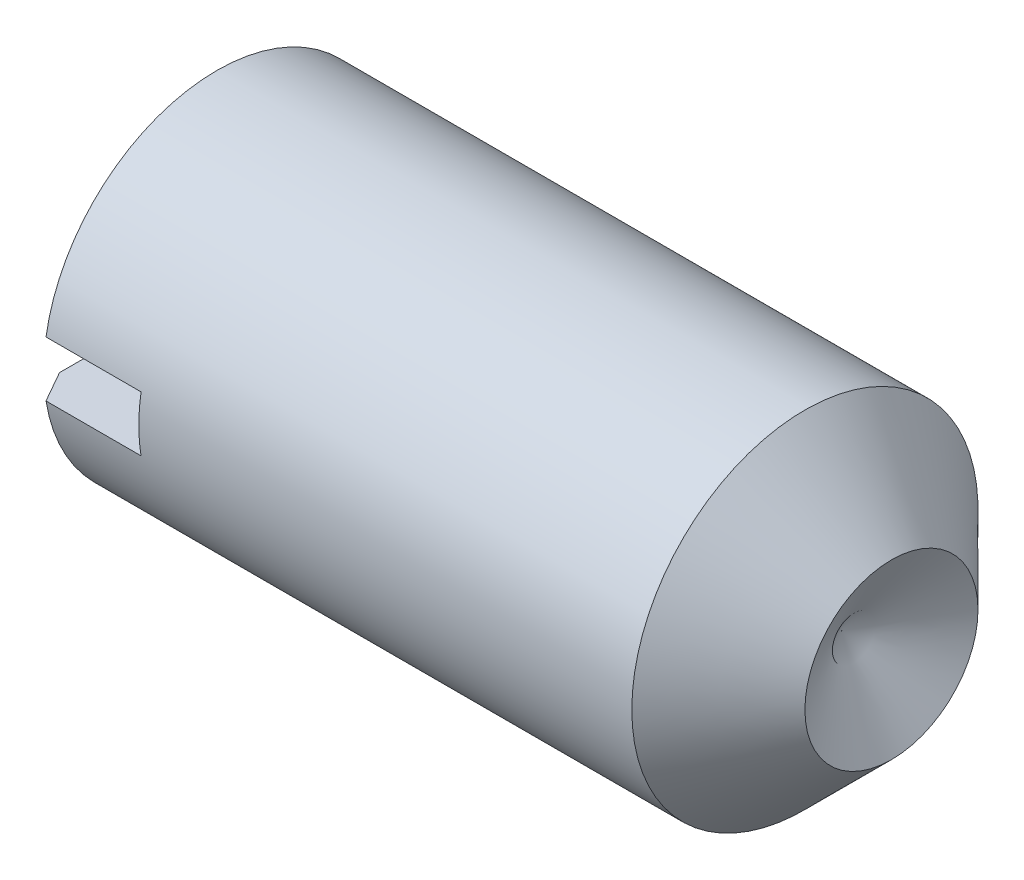
SolidWorks part; units mm, degrees
ref_plane "Plane1" through (0, 0, 0) normal (0, 0, 1) x (1, 0, 0)
ref_plane "Plane2" through (0, 0, 0) normal (0, 1, 0) x (1, 0, 0)
ref_plane "Plane3" through (0, 0, 0) normal (1, 0, 0) x (0, 0, -1)
sketch "BodySke" plane through (0, 0, 0) normal (0, 0, 1) x (1, 0, 0)
  line L0 (0.2569, -2.5) -> (47.1574, -2.5) construction
  line L1 (10, 1.25) -> (9.2783, 0)
  line L2 (0.2569, 2.5) -> (8.75, 2.5)
  line L3 (10, 1.25) -> (8.75, 2.5)
  line L4 (9.2783, 0) -> (0, 0)
  line L5 (-12.7, 0) -> (88.9, 0) construction
  line L6 (10, 1.25) -> (10, 19.05) construction
  line L7 (10, -1.25) -> (8.75, -2.5) construction
  line L8 (0.8, 12.7) -> (0.8, -3.175) construction
  line L9 (0, 0) -> (0, 2.055)
  line L10 (0, 2.055) -> (0.2569, 2.5)
  line L11 (0, -2.055) -> (0.2569, -2.5) construction
  line L12 (10, -1.25) -> (9.2783, 0) construction
  dimension "Length" = 10
  dimension "Diameter" = 5
  dimension "Drive_ch_ang" = 60
  dimension "Cup_ang" = 120
  dimension "Cup_dia" = 2.5
  dimension "Nose_ch_ang" = 45
  dimension "Advance" = 0.8
  dimension "Minor_dia" = 4.11
revolve "BaseBody" add sketch "BodySke"
cosmetic thread "ThreadCosmetic" [suppressed]
extrude "Slot" cut sketch "Sketch2" along normal blind 1.63
sketch "Sketch2" plane through (0, 0, 0) normal (1, 0, 0) x (0, 0, -1)
  line L1 (2.5, -0.4) -> (-2.5, -0.4)
  line L2 (2.5, -0.4) -> (2.5, 0.4)
  line L3 (2.5, 0.4) -> (-2.5, 0.4)
  line L4 (-2.5, -0.4) -> (-2.5, 0.4)
  dimension "D1" = 5
  dimension "D2" = 0.4
  dimension "Slot_width" = 0.8
  dimension "D3" = 2.5
sketch "ThdSchSke" plane through (0, 0, 0) normal (0, 0, 1) x (1, 0, 0)
  line L0 (0.2569, -2.055) -> (-0.0547, -2.5)
  line L1 (0.2569, -2.055) -> (0.5685, -2.5)
  line L2 (0.5685, -2.5) -> (0.5685, -3.125)
  line L3 (-3.175, 0) -> (5.1513, 0) construction
  line L5 (0.5685, -3.125) -> (-0.0547, -3.125)
  line L6 (-0.0547, -3.125) -> (-0.0547, -2.5)
  line L7 (0.2569, -2.5) -> (0.2569, -0.4) construction
  dimension "Thread_minor" = 4.11
  dimension "Diameter" = 5
  dimension "SideAngle" = 55
  dimension "VeeAngle" = 70
  dimension "Overcut" = 6.25
revolve "ThreadSchematic" [suppressed] cut sketch "ThdSchSke" angle 360 about L3
pattern_linear "ThdSchPat" [suppressed]
equation "\"D1@Sketch2\" = \"Diameter@BodySke\""
equation "\"D3@Sketch2\" = \"D1@Sketch2\" / 2"
equation "\"D2@Sketch2\" = \"Slot_width@Sketch2\" / 2"
equation "\"Thread_minor@ThdSchSke\" = \"Minor_dia@BodySke\""
equation "\"Diameter@ThdSchSke\" = \"Diameter@BodySke\""
equation "\"Overcut@ThdSchSke\" = \"Diameter@BodySke\" * 1.25"
equation "\"Num_threads@ThdSchPat\" = int( (\"Length@BodySke\" - ( ( ( \"Diameter@BodySke\" - \"Minor_dia@BodySke\" ) * 0.5 ) / tan( \"Drive_ch_ang@BodySke\" * 0.017453292 ) ) - ( ( ( \"Diameter@BodySke\" - \"Cup_dia@BodySke\" ) * 0.5 ) * tan( \"Nose_ch_ang@BodySke\" * 0.017453292 ) ) ) / \"Advance@BodySke\" + 0.999 )  + 1"
equation "\"Advance@ThdSchPat\" = (\"Length@BodySke\" - ( ( ( \"Diameter@BodySke\" - \"Minor_dia@BodySke\" ) * 0.5 ) / tan( \"Drive_ch_ang@BodySke\" * 0.017453292 ) ) - ( ( ( \"Diameter@BodySke\" - \"Cup_dia@BodySke\" ) * 0.5 ) * tan( \"Nose_ch_ang@BodySke\" * 0.017453292 ) ) ) /  (\"Num_threads@ThdSchPat\" - 1) 'relax it"
equation "' \"Num_threads@ThdSchPat\" = \"Num_threads@ThdSchPat\" - sgn( \"Num_threads@ThdSchPat\" - 1) '---chamfered tips only---"
